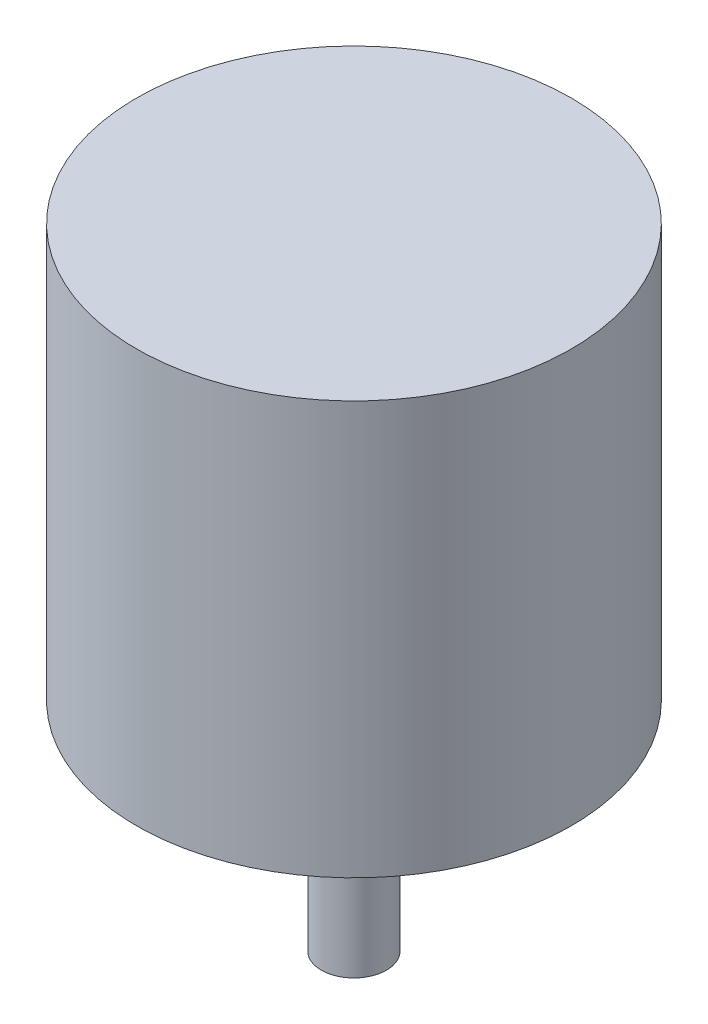
SolidWorks part; units mm, degrees
ref_plane "Plano frontal" through (0, 0, 0) normal (0, 0, 1) x (1, 0, 0)
ref_plane "Plano superior" through (0, 0, 0) normal (0, 1, 0) x (1, 0, 0)
ref_plane "Plano direito" through (0, 0, 0) normal (1, 0, 0) x (0, 0, -1)
ref_plane "Plano1" through (0, 0, 0) normal (0, -1, 0) x (1, 0, 0)
sketch "Esboço11" plane through (0, 0, 0) normal (0, -1, 0) x (1, 0, 0)
  circle A0 centre (0, 0) radius 20
extrude "Ressalto-extrusão3" add sketch "Esboço11" along normal blind 38
sketch "Esboço12" plane through (0, -38, 0) normal (0, -1, 0) x (1, 0, 0)
  circle A0 centre (0, 0) radius 10
extrude "Ressalto-extrusão4" add sketch "Esboço12" along normal blind 5
sketch "Esboço13" plane through (0, -43, 0) normal (0, -1, 0) x (1, 0, 0)
  circle A0 centre (0, 0) radius 3
extrude "Ressalto-extrusão5" add sketch "Esboço13" along normal blind 15
